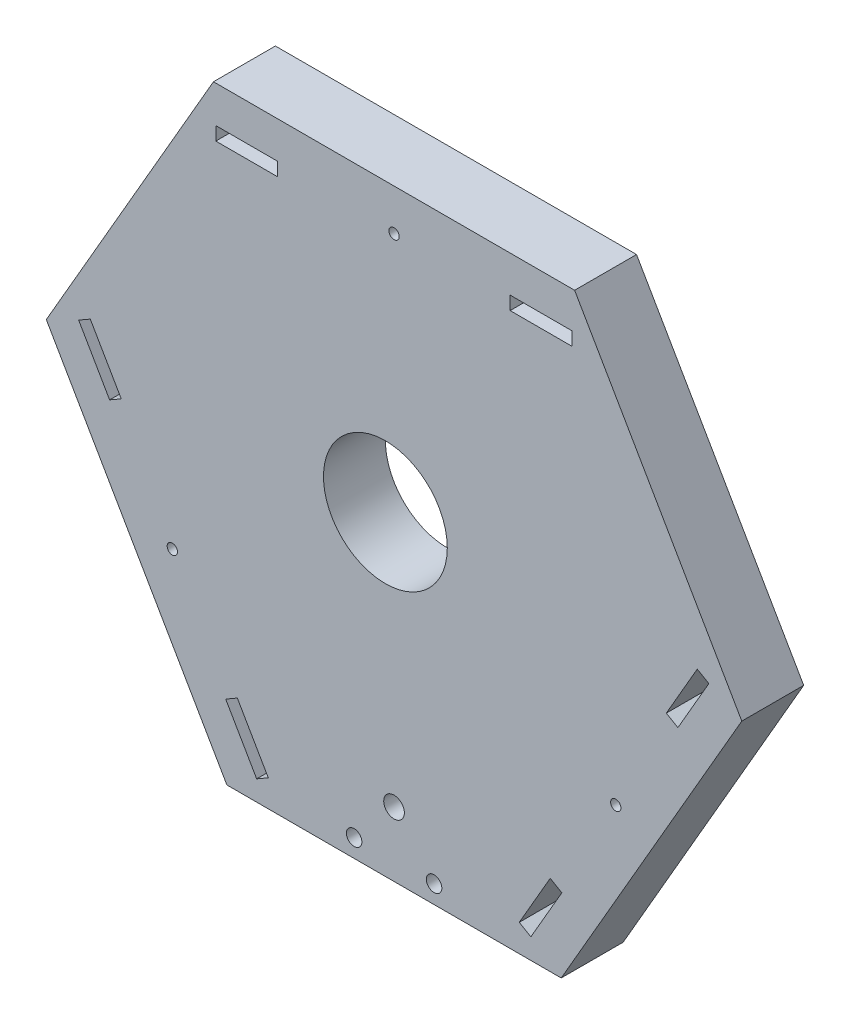
SolidWorks part; units mm, degrees
ref_plane "Plano frontal" through (0, 0, 0) normal (0, 0, 1) x (1, 0, 0)
ref_plane "Plano superior" through (0, 0, 0) normal (0, 1, 0) x (1, 0, 0)
ref_plane "Plano direito" through (0, 0, 0) normal (1, 0, 0) x (0, 0, -1)
sketch "Model" plane through (0, 0, 0) normal (0, 0, 1) x (1, 0, 0)
  line L0 (312.4019, 240.8782) -> (347.4019, 301.5)
  line L1 (347.4019, 301.5) -> (315, 357.6218)
  line L2 (315, 357.6218) -> (245, 357.6218)
  line L3 (245, 357.6218) -> (212.5981, 301.5)
  line L4 (212.5981, 301.5) -> (247.5981, 240.8782)
  line L5 (247.5981, 240.8782) -> (312.4019, 240.8782)
  line L6 (245.4531, 350.4867) -> (257.4531, 350.4867)
  line L7 (245.4531, 347.8867) -> (245.4531, 350.4867)
  line L8 (314.5, 350.5596) -> (302.5, 350.5596)
  line L9 (314.5, 347.9596) -> (314.5, 350.5596)
  line L10 (332.7685, 295.5164) -> (335.0202, 294.2164)
  line L11 (338.7685, 305.9087) -> (341.0202, 304.6087)
  line L12 (310.2721, 256.5432) -> (312.5238, 255.2432)
  line L13 (304.2685, 246.1529) -> (306.5202, 244.8529)
  line L14 (255.6232, 246.0904) -> (253.3716, 244.7904)
  line L15 (249.6232, 256.4827) -> (247.3716, 255.1827)
  line L16 (227.1232, 295.4539) -> (224.8716, 294.1539)
  line L17 (221.1232, 305.8462) -> (218.8716, 304.5462)
  line L18 (221.1232, 305.8462) -> (227.1232, 295.4539)
  line L19 (249.6232, 256.4827) -> (255.6232, 246.0904)
  line L20 (304.2685, 246.1529) -> (310.2721, 256.5432)
  line L21 (332.7685, 295.5164) -> (338.7685, 305.9087)
  line L22 (302.5, 350.5596) -> (302.5, 347.9596)
  line L23 (245.4531, 347.8867) -> (257.4531, 347.8867)
  line L24 (218.8716, 304.5462) -> (224.8716, 294.1539)
  line L25 (247.3716, 255.1827) -> (253.3716, 244.7904)
  line L26 (312.5238, 255.2432) -> (306.5202, 244.8529)
  line L27 (257.4531, 347.8867) -> (257.4531, 350.4867)
  line L28 (302.5, 347.9596) -> (314.5, 347.9596)
  line L29 (335.0202, 294.2164) -> (341.0202, 304.6087)
  circle A0 centre (280, 253.3782) radius 2
  circle A1 centre (272.2603, 244.389) radius 1.5
  circle A2 centre (287.7603, 244.389) radius 1.5
  circle A9 centre (280, 349.6218) radius 1
  circle A10 centre (237.0263, 275.1891) radius 1
  circle A11 centre (322.9737, 275.1891) radius 1
  circle A13 centre (278.324, 302.0322) radius 12
  dimension "D1" = 134.8038
  dimension "D2" = 5.2099
  dimension "D3" = 12
  dimension "D4" = 2.6
  dimension "D5" = 5.2122
  dimension "D6" = 12
  dimension "D7" = 2.6
  dimension "D8" = 45
  dimension "D9" = 3.9747
  dimension "D10" = 12
  dimension "D11" = 3.9724
  dimension "D12" = 12
  dimension "D13" = 2.6
  dimension "D14" = 2.6
  dimension "D15" = 45
  dimension "D16" = 3.96
  dimension "D17" = 3.9641
  dimension "D18" = 12
  dimension "D20" = 2.6
  dimension "D21" = 12
  dimension "D22" = 2.6
sketch "Esboço1" plane through (0, 0, 0) normal (0, 0, 1) x (1, 0, 0)
  line L0 (312.4019, 240.8782) -> (347.4019, 301.5)
  line L1 (347.4019, 301.5) -> (315, 357.6218)
  line L2 (315, 357.6218) -> (245, 357.6218)
  line L3 (245, 357.6218) -> (212.5981, 301.5)
  line L4 (212.5981, 301.5) -> (247.5981, 240.8782)
  line L5 (247.5981, 240.8782) -> (312.4019, 240.8782)
  line L6 (245.4531, 350.4867) -> (257.4531, 350.4867)
  line L7 (245.4531, 347.8867) -> (245.4531, 350.4867)
  line L8 (314.5, 350.5596) -> (302.5, 350.5596)
  line L9 (314.5, 347.9596) -> (314.5, 350.5596)
  line L10 (332.7685, 295.5164) -> (335.0202, 294.2164)
  line L11 (338.7685, 305.9087) -> (341.0202, 304.6087)
  line L12 (310.2721, 256.5432) -> (312.5238, 255.2432)
  line L13 (304.2685, 246.1529) -> (306.5202, 244.8529)
  line L14 (255.6232, 246.0904) -> (253.3716, 244.7904)
  line L15 (249.6232, 256.4827) -> (247.3716, 255.1827)
  line L16 (227.1232, 295.4539) -> (224.8716, 294.1539)
  line L17 (221.1232, 305.8462) -> (218.8716, 304.5462)
  line L18 (221.1232, 305.8462) -> (227.1232, 295.4539)
  line L19 (249.6232, 256.4827) -> (255.6232, 246.0904)
  line L20 (304.2685, 246.1529) -> (310.2721, 256.5432)
  line L21 (332.7685, 295.5164) -> (338.7685, 305.9087)
  line L22 (302.5, 350.5596) -> (302.5, 347.9596)
  line L23 (245.4531, 347.8867) -> (257.4531, 347.8867)
  line L24 (218.8716, 304.5462) -> (224.8716, 294.1539)
  line L25 (247.3716, 255.1827) -> (253.3716, 244.7904)
  line L26 (312.5238, 255.2432) -> (306.5202, 244.8529)
  line L27 (257.4531, 347.8867) -> (257.4531, 350.4867)
  line L28 (302.5, 347.9596) -> (314.5, 347.9596)
  line L29 (335.0202, 294.2164) -> (341.0202, 304.6087)
  circle A0 centre (280, 253.3782) radius 2
  circle A1 centre (272.2603, 244.389) radius 1.5
  circle A2 centre (287.7603, 244.389) radius 1.5
  circle A3 centre (280, 349.6218) radius 1
  circle A4 centre (237.0263, 275.1891) radius 1
  circle A5 centre (322.9737, 275.1891) radius 1
  circle A6 centre (278.324, 302.0322) radius 12
  dimension "D1" = 134.8038
  dimension "D2" = 5.2099
  dimension "D3" = 12
  dimension "D4" = 2.6
  dimension "D5" = 5.2122
  dimension "D6" = 12
  dimension "D7" = 2.6
  dimension "D8" = 45
  dimension "D9" = 3.9747
  dimension "D10" = 12
  dimension "D11" = 3.9724
  dimension "D12" = 12
  dimension "D13" = 2.6
  dimension "D14" = 2.6
  dimension "D15" = 45
  dimension "D16" = 3.96
  dimension "D17" = 3.9641
  dimension "D18" = 12
  dimension "D19" = 2.6
  dimension "D20" = 12
  dimension "D21" = 2.6
extrude "Ressalto-extrusão1" add sketch "Esboço1" along normal blind 12
